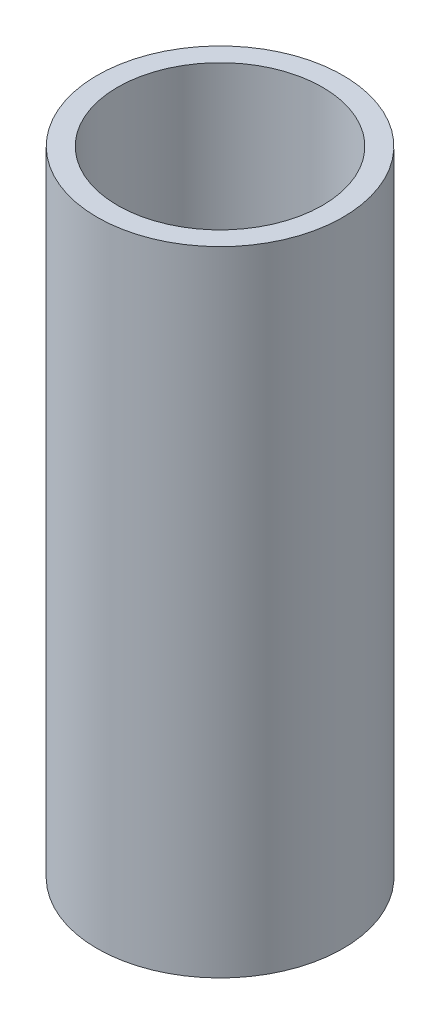
SolidWorks part; units mm, degrees
material "PLA"
ref_plane "Front Plane" through (0, 0, 0) normal (0, 0, 1) x (1, 0, 0)
ref_plane "Top Plane" through (0, 0, 0) normal (0, 1, 0) x (1, 0, 0)
ref_plane "Right Plane" through (0, 0, 0) normal (1, 0, 0) x (0, 0, -1)
sketch "Sketch1" plane through (0, 0, 0) normal (0, 1, 0) x (1, 0, 0)
  circle A0 centre (0, 0) radius 1.625
  circle A1 centre (0, 0) radius 1.95
  dimension "D1" = 3.25
  dimension "D2" = 3.9
extrude "Boss-Extrude1" add sketch "Sketch1" along normal mid plane 10.048
